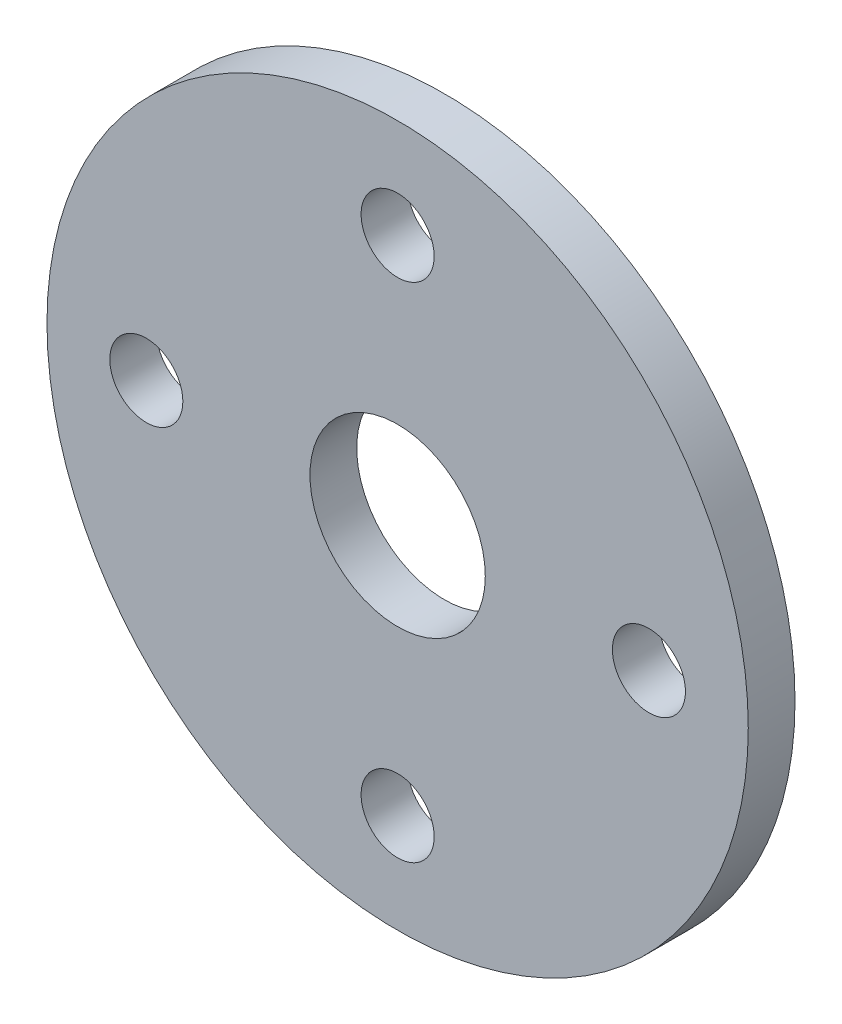
SolidWorks part; units mm, degrees
material "Acier non allié"
ref_plane "Plan de face" through (0, 0, 0) normal (0, 0, 1) x (1, 0, 0)
ref_plane "Plan de dessus" through (0, 0, 0) normal (0, 1, 0) x (1, 0, 0)
ref_plane "Plan de droite" through (0, 0, 0) normal (1, 0, 0) x (0, 0, -1)
sketch "Esquisse1" plane through (0, 0, 0) normal (0, 0, 1) x (1, 0, 0)
  line L0 (0, 0) -> (-43, 0) construction
  line L1 (-43, 0) -> (0, 43) construction
  line L2 (0, -43) -> (0, 0) construction
  line L3 (0, 0) -> (43, 0) construction
  line L4 (0, 43) -> (43, 0) construction
  line L5 (0, 43) -> (0, 0) construction
  line L6 (43, 0) -> (0, -43) construction
  line L7 (0, -43) -> (-43, 0) construction
  circle A0 centre (0, 0) radius 60
  circle A1 centre (0, 0) radius 43 construction
  circle A2 centre (0, 0) radius 15
  circle A3 centre (0, 43) radius 6.25
  circle A4 centre (-43, 0) radius 6.25
  circle A5 centre (0, -43) radius 6.25
  circle A6 centre (43, 0) radius 6.25
  dimension "D1" = 30
  dimension "D2" = 86
  dimension "D3" = 120
  dimension "D4" = 12.5
extrude "Boss.-Extru.1" add sketch "Esquisse1" along normal mid plane 8
